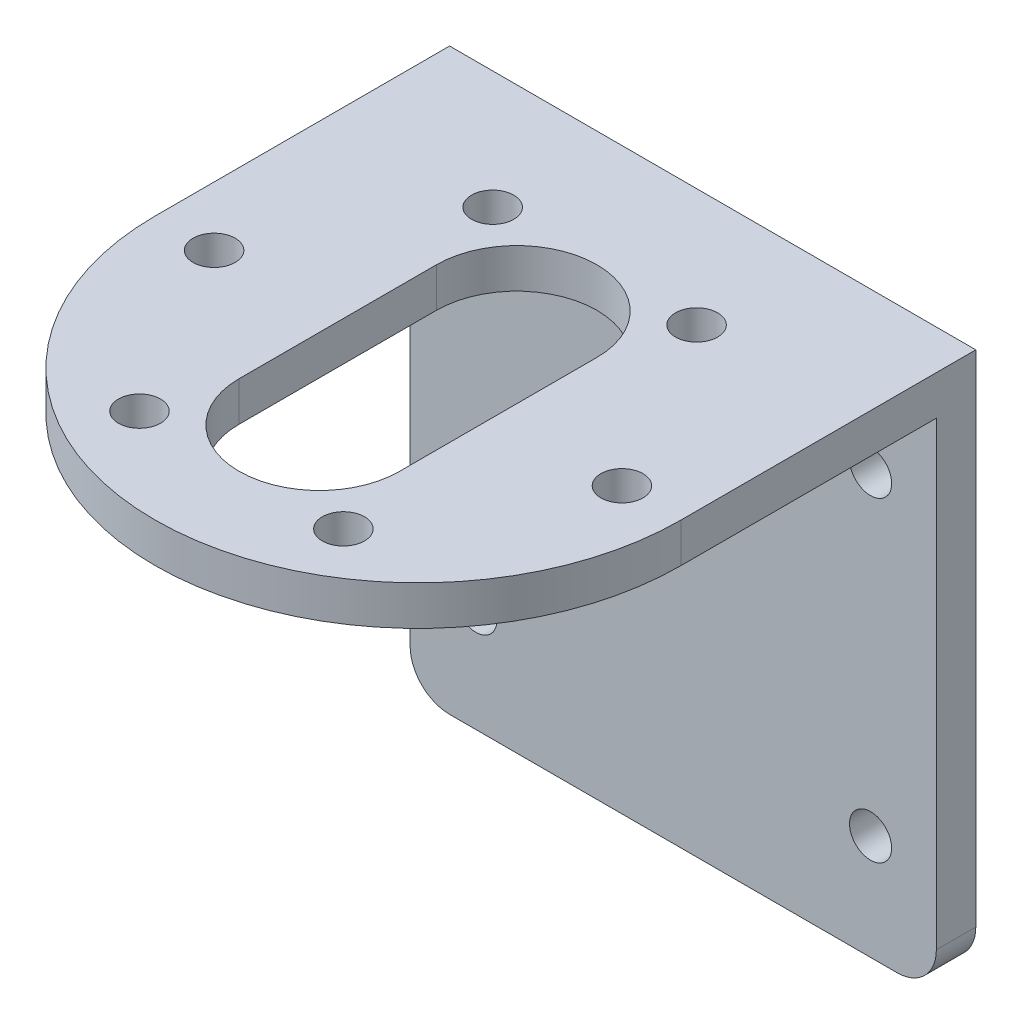
SolidWorks part; units mm, degrees
ref_plane "前视基准面" through (0, 0, 0) normal (0, 0, 1) x (1, 0, 0)
ref_plane "上视基准面" through (0, 0, 0) normal (0, 1, 0) x (1, 0, 0)
ref_plane "右视基准面" through (0, 0, 0) normal (1, 0, 0) x (0, 0, -1)
other "Configuration Table"
sketch "草图2" plane through (0, 0, 0) normal (0, 0, 1) x (1, 0, 0)
  line L0 (-14.6137, -6.4501) -> (-14.6137, 17.5499) construction
  line L1 (-19.6137, 26.5499) -> (20.3863, 26.5499)
  line L2 (-19.6137, 26.5499) -> (-19.6137, -14.4501)
  line L3 (-19.6137, -14.4501) -> (20.3863, -14.4501)
  line L4 (20.3863, 26.5499) -> (20.3863, -14.4501)
  line L5 (15.3863, -6.4501) -> (15.3863, 17.5499) construction
  line L6 (-14.6137, -6.4501) -> (15.3863, -6.4501) construction
  line L7 (15.3863, 17.5499) -> (-14.6137, 17.5499) construction
  circle A0 centre (-14.6137, -6.4501) radius 1.6
  circle A1 centre (15.3863, -6.4501) radius 1.6
  circle A2 centre (-14.6137, 17.5499) radius 1.6
  circle A3 centre (15.3863, 17.5499) radius 1.6
  point P12 (0.3863, -6.4501)
  point P13 (0.3863, -14.4501)
  dimension "D3" = 3.2
  dimension "D1" = 40
  dimension "D2" = 41
  dimension "D4" = 8
  dimension "D5" = 24
  dimension "D6" = 30
extrude "凸台-拉伸1" add sketch "草图2" along normal blind 44.2
sketch "草图3" plane through (0, 0, 44.2) normal (0, 0, 1) x (1, 0, 0)
  line L0 (20.3863, -14.4501) -> (20.3863, 26.5499) construction
  line L1 (-19.6137, 23.5499) -> (20.3863, 23.5499)
  line L2 (-19.6137, 23.5499) -> (-19.6137, -14.4501)
  line L3 (-19.6137, -14.4501) -> (20.3863, -14.4501)
  line L4 (20.3863, 23.5499) -> (20.3863, -14.4501)
  line L5 (-19.6137, 26.5499) -> (-19.6137, -14.4501) construction
  line L6 (-19.6137, -14.4501) -> (20.3863, -14.4501) construction
  line L7 (20.3863, 26.5499) -> (-19.6137, 26.5499) construction
  dimension "D1" = 3
extrude "切除-拉伸1" cut sketch "草图3" against normal blind 41.2
sketch "草图4" plane through (0, 23.5499, 0) normal (0, -1, 0) x (1, 0, 0)
  line L0 (-19.6137, 0) -> (20.3863, 0) construction
  line L1 (20.3863, 3) -> (-19.6137, 3) construction
  line L2 (-19.6137, 3) -> (-19.6137, 44.2) construction
  line L3 (-19.6137, 44.2) -> (20.3863, 44.2)
  line L4 (-19.6137, 44.2) -> (-19.6137, 22.4)
  line L6 (20.3863, 44.2) -> (20.3863, 22.4)
  line L7 (20.3863, 44.2) -> (-19.6137, 44.2) construction
  line L8 (20.3863, 3) -> (20.3863, 44.2) construction
  line L9 (0.3863, 22.4) -> (0.3863, 37.9) construction
  line L10 (8.1363, 35.8234) -> (0.3863, 22.4) construction
  line L11 (0.3863, 22.4) -> (15.8863, 22.4) construction
  line L12 (0.3863, 22.4) -> (-7.3637, 8.9766) construction
  line L13 (8.1363, 8.9766) -> (0.3863, 22.4) construction
  line L14 (-7.3637, 35.8234) -> (0.3863, 22.4) construction
  line L15 (0.3863, 22.4) -> (-15.1137, 22.4) construction
  line L16 (0.3863, 14.9) -> (0.3863, 29.9) construction
  line L17 (-5.7137, 14.9) -> (-5.7137, 29.9)
  line L18 (6.4863, 14.9) -> (6.4863, 29.9)
  arc A0 (20.3863, 22.4) -> (-19.6137, 22.4) centre (0.3863, 22.4) ccw
  circle A1 centre (0.3863, 22.4) radius 15.5 construction
  circle A2 centre (-7.3637, 35.8234) radius 1.6
  circle A3 centre (8.1363, 35.8234) radius 1.6
  circle A4 centre (15.8863, 22.4) radius 1.6
  circle A5 centre (8.1363, 8.9766) radius 1.6
  circle A6 centre (-7.3637, 8.9766) radius 1.6
  circle A7 centre (-15.1137, 22.4) radius 1.6
  circle A9 centre (0.3863, 22.4) radius 18.5 construction
  arc A10 (-5.7137, 14.9) -> (6.4863, 14.9) centre (0.3863, 14.9) ccw
  arc A11 (6.4863, 29.9) -> (-5.7137, 29.9) centre (0.3863, 29.9) ccw
  point P7 (0.3863, 3)
  point P33 (0.3863, 22.4)
  dimension "D1" = 22.4
  dimension "D2" = 40
  dimension "D3" = 31
  dimension "D4" = 3.2
  dimension "D8" = 37
  dimension "D9" = 6.1
  dimension "D5" = 60
  dimension "D6" = 60
  dimension "D7" = 30
  dimension "D10" = 15
fillet "圆角1" radius 3 2 edges at (20.3863, -14.4501, 1.5) (-19.6137, -14.4501, 1.5)
extrude "切除-拉伸2" cut sketch "草图4" against normal blind 10
